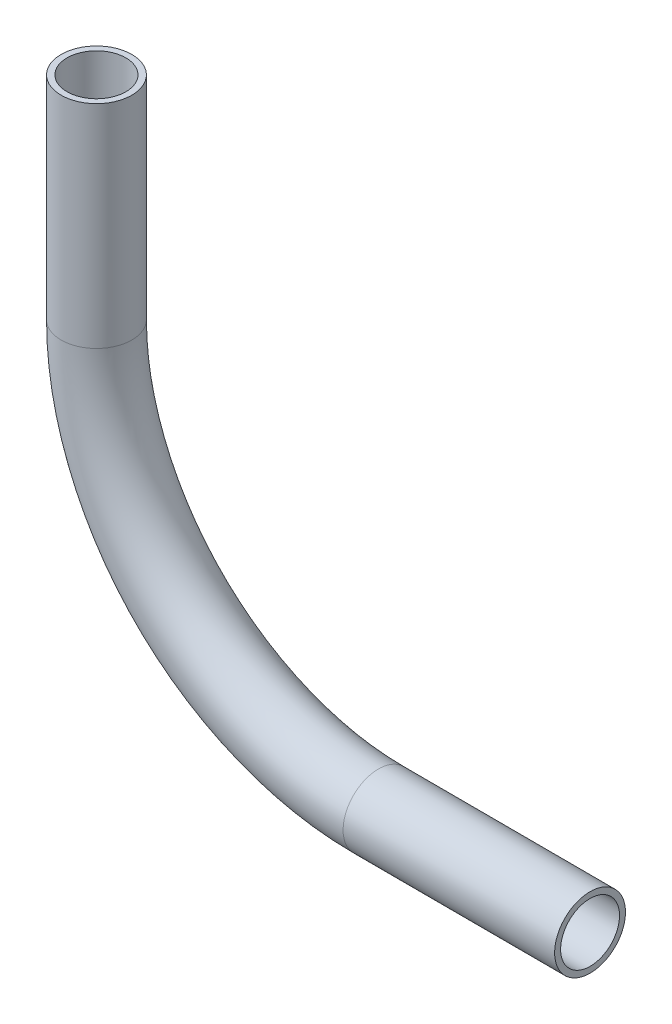
SolidWorks part; units mm, degrees
ref_plane "Front Plane" through (0, 0, 0) normal (0, 0, 1) x (1, 0, 0)
ref_plane "Top Plane" through (0, 0, 0) normal (0, 1, 0) x (1, 0, 0)
ref_plane "Right Plane" through (0, 0, 0) normal (1, 0, 0) x (0, 0, -1)
sketch3d "3DSketch1"
  line L0 (44.5241, -623.1164, 354.9277) -> (44.5241, -661.2164, 354.9277)
  line L1 (95.324, -712.0164, 355.047) -> (133.4239, -712.0164, 355.1365)
  arc A2 (44.5241, -661.2164, 354.9277) -> (95.324, -712.0164, 355.047) centre (95.324, -661.2164, 355.047) ccw
  point P13 (44.5241, -712.0164, 354.9277)
  point P14 (95.2047, -661.2164, 405.8469)
  dimension "D1" = 50.8
  dimension "D2" = 38.1
  dimension "D3" = 38.1
other "Pipe 0.5 SCH 40(1)"
ref_plane "Plane1" through (44.5241, -623.1164, 354.9277) normal (0, -1, 0) x (1, 0, 0)
sketch "Sketch1" plane through (44.5241, -623.1164, 354.9277) normal (0, -1, 0) x (1, 0, 0)
  circle A0 centre (0, 0) radius 5.2832
  circle A1 centre (0, 0) radius 6.35
  point P5 (0, 0)
  dimension "In_dia" = 10.5664
  dimension "Out_dia" = 12.7
